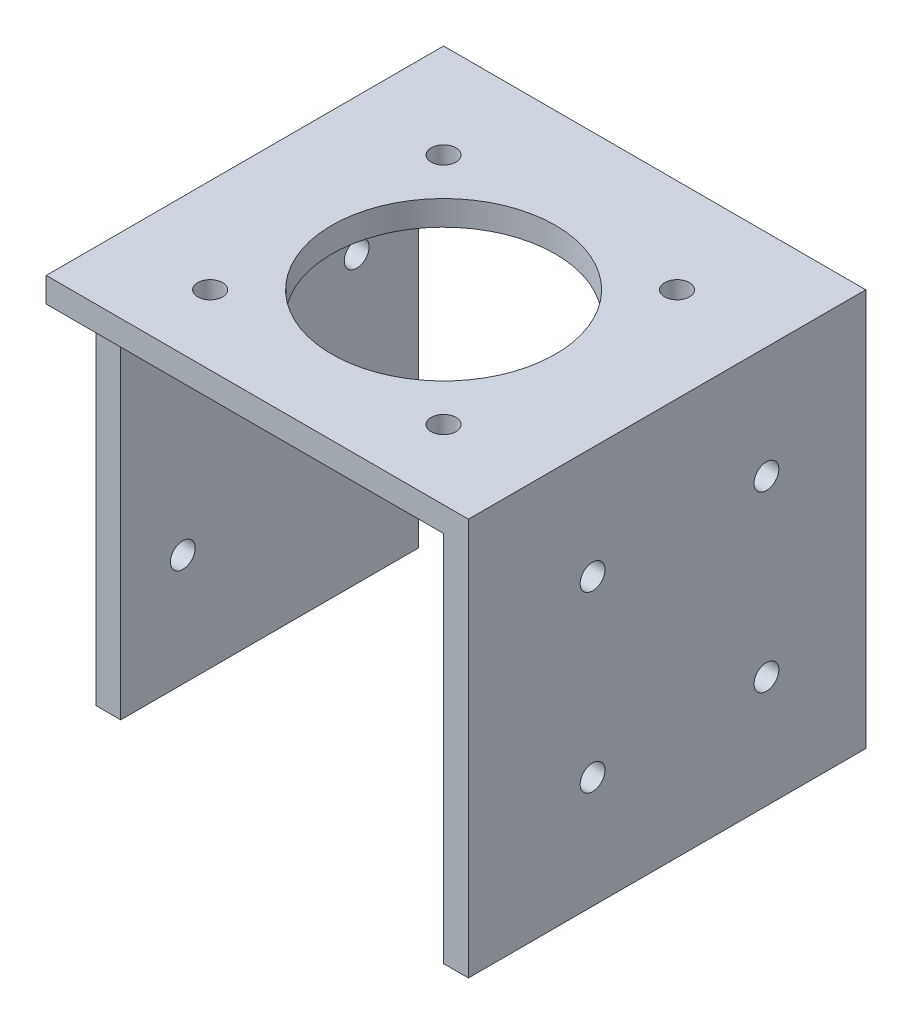
SolidWorks part; units mm, degrees
material "5052-H32"
ref_plane "Front Plane" through (0, 0, 0) normal (0, 0, 1) x (1, 0, 0)
ref_plane "Top Plane" through (0, 0, 0) normal (0, 1, 0) x (1, 0, 0)
ref_plane "Right Plane" through (0, 0, 0) normal (1, 0, 0) x (0, 0, -1)
sketch "Sketch1" plane through (0, 0, 0) normal (0, 0, 1) x (1, 0, 0)
  line L1 (-40, 40) -> (40, 40)
  line L2 (-40, 40) -> (-40, -40)
  line L3 (-40, -40) -> (40, -40)
  line L4 (40, 40) -> (40, -40)
  line L5 (-40, 40) -> (40, -40) construction
  line L6 (-40, -40) -> (40, 40) construction
  point P0 (0, 0)
  dimension "D1" = 80
  dimension "D2" = 80
extrude "Boss-Extrude1" add sketch "Sketch1" along normal blind 80
sketch "Sketch2" plane through (0, 0, 80) normal (0, 0, 1) x (1, 0, 0)
  line L0 (-40, 35) -> (35, 35)
  line L1 (-40, 40) -> (-40, -40) construction
  line L2 (35, 35) -> (35, -40)
  line L3 (-40, -40) -> (40, -40) construction
  line L4 (35, -40) -> (-40, -40)
  line L5 (-40, -40) -> (-40, 35)
  dimension "D1" = 75
  dimension "D2" = 75
extrude "Cut-Extrude1" cut sketch "Sketch2" against normal blind 75
sketch "Sketch3" plane through (35, 0, 0) normal (-1, 0, 0) x (0, 0, 1)
  line L3 (80, 40) -> (0, 40) construction
  line L4 (0, -40) -> (0, 40) construction
  circle A0 centre (55, -17.5) radius 2.5
  circle A1 centre (20, -17.5) radius 2.5
  circle A2 centre (20, 17.5) radius 2.5
  circle A3 centre (55, 17.5) radius 2.5
  dimension "D1" = 5
  dimension "D2" = 5
  dimension "D3" = 5
  dimension "D4" = 5
  dimension "D5" = 35
  dimension "D6" = 20
  dimension "D7" = 35
  dimension "D8" = 35
  dimension "D9" = 20
  dimension "D10" = 35
  dimension "D11" = 22.5
  dimension "D12" = 22.5
extrude "Cut-Extrude2" cut sketch "Sketch3" against normal blind 50
sketch "Sketch4" plane through (0, 35, 0) normal (0, -1, 0) x (1, 0, 0)
  line L5 (-40, 5) -> (-40, 80) construction
  line L6 (35, 80) -> (-40, 80) construction
  circle A0 centre (-26, 66) radius 2.5
  circle A1 centre (21, 66) radius 2.5
  circle A2 centre (-26, 19) radius 2.5
  circle A3 centre (21, 19) radius 2.5
  dimension "D1" = 5
  dimension "D2" = 5
  dimension "D3" = 5
  dimension "D4" = 5
  dimension "D5" = 47
  dimension "D6" = 47
  dimension "D7" = 47
  dimension "D8" = 14
  dimension "D9" = 14
  dimension "D10" = 14
  dimension "D11" = 14
  dimension "D12" = 47
extrude "Cut-Extrude3" cut sketch "Sketch4" against normal blind 50
sketch "Sketch5" plane through (0, 35, 0) normal (0, -1, 0) x (1, 0, 0)
  line L1 (35, 5) -> (35, 80) construction
  line L2 (35, 80) -> (-40, 80) construction
  circle A0 centre (-2.5, 42.5) radius 22.5
  dimension "D1" = 37.5
  dimension "D3" = 45
  dimension "D2" = 37.5
extrude "Cut-Extrude4" cut sketch "Sketch5" against normal blind 50
sketch "Sketch8" plane through (-40, 0, 0) normal (-1, 0, 0) x (0, 0, 1)
  line L0 (0, 40) -> (80, 40)
  line L1 (80, 40) -> (80, -40)
  line L2 (80, -40) -> (0, -40)
  line L3 (0, -40) -> (0, 40)
extrude "Boss-Extrude2" add sketch "Sketch8" along normal blind 5
sketch "Sketch9" plane through (-45, 0, 0) normal (-1, 0, 0) x (0, 0, 1)
  line L1 (80, -40) -> (80, 40) construction
  line L4 (0, -40) -> (80, -40) construction
  line L5 (0, 40) -> (0, -40) construction
  circle A4 centre (22.5, 17.5) radius 2.5
  circle A5 centre (57.5, 17.5) radius 2.5
  circle A6 centre (22.5, -17.5) radius 2.5
  circle A7 centre (57.5, -17.5) radius 2.5
  dimension "D1" = 5
  dimension "D2" = 5
  dimension "D3" = 5
  dimension "D4" = 5
  dimension "D5" = 35
  dimension "D6" = 35
  dimension "D7" = 35
  dimension "D8" = 35
  dimension "D9" = 22.5
  dimension "D10" = 22.5
  dimension "D11" = 22.5
  dimension "D12" = 22.5
extrude "Cut-Extrude5" cut sketch "Sketch9" against normal blind 5
sketch "Sketch10" plane through (0, -40, 0) normal (0, -1, 0) x (1, 0, 0)
  line L0 (-45, 80) -> (-40, 80)
  line L1 (-40, 80) -> (-40, 70)
  line L2 (-40, 5) -> (-40, 80) construction
  line L3 (-40, 70) -> (-45, 70)
  line L4 (-45, 0) -> (-45, 80) construction
  line L5 (-45, 70) -> (-45, 80)
  line L6 (-45, 10) -> (-40, 10)
  line L7 (-40, 5) -> (-40, 80) construction
  line L8 (-40, 10) -> (-40, 0)
  line L9 (-45, 0) -> (40, 0) construction
  line L10 (-40, 0) -> (-45, 0)
  line L11 (-45, 0) -> (-45, 10)
  dimension "D1" = 10
  dimension "D2" = 10
extrude "Cut-Extrude6" cut sketch "Sketch10" against normal blind 75
sketch "Sketch11" plane through (-40, 0, 0) normal (-1, 0, 0) x (0, 0, 1)
  line L0 (0, 35) -> (5, 35)
  line L1 (10, 35) -> (0, 35) construction
  line L2 (5, 35) -> (5, -40)
  line L3 (5, -40) -> (0, -40)
  line L4 (0, -40) -> (0, 35)
extrude "Cut-Extrude7" cut sketch "Sketch11" against normal blind 75
